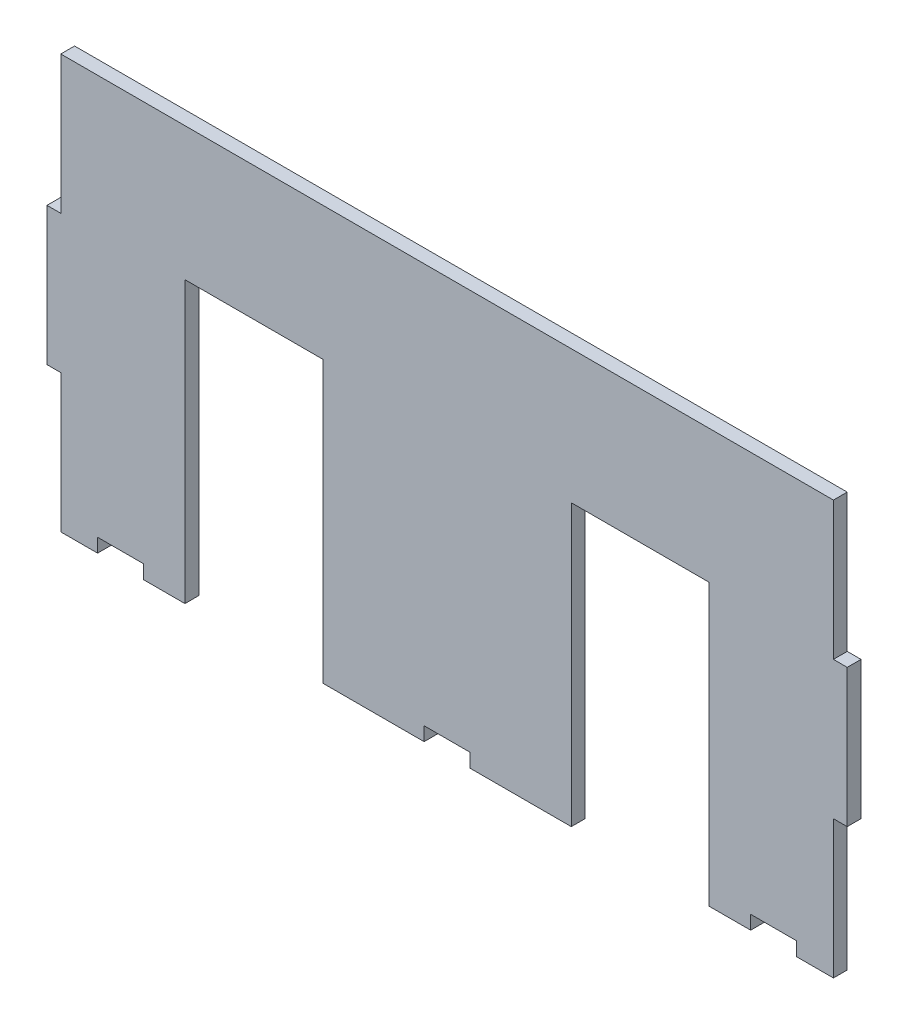
SolidWorks part; units mm, degrees
ref_plane "Front Plane" through (0, 0, 0) normal (0, 0, 1) x (1, 0, 0)
ref_plane "Top Plane" through (0, 0, 0) normal (0, 1, 0) x (1, 0, 0)
ref_plane "Right Plane" through (0, 0, 0) normal (1, 0, 0) x (0, 0, -1)
sketch "Model" plane through (0, 0, 0) normal (0, 0, 1) x (1, 0, 0)
  line L0 (178.1905, 199.1238) -> (178.1905, 169.1238)
  line L1 (352.1905, 199.1238) -> (352.1905, 169.1238)
  line L2 (322.1905, 139.1238) -> (322.1905, 200.1238)
  line L3 (322.1905, 200.1238) -> (292.1905, 200.1238)
  line L4 (292.1905, 200.1238) -> (292.1905, 139.1238)
  line L5 (181.1905, 229.1238) -> (349.1905, 229.1238)
  line L13 (181.1905, 139.1238) -> (189.1905, 139.1238)
  line L16 (189.1905, 139.1238) -> (189.1905, 142.1238)
  line L18 (189.1905, 142.1238) -> (199.1905, 142.1238)
  line L19 (208.1905, 139.1238) -> (199.1905, 139.1238)
  line L20 (199.1905, 139.1238) -> (199.1905, 142.1238)
  line L21 (238.1905, 139.1238) -> (260.1905, 139.1238)
  line L22 (260.1905, 139.1238) -> (260.1905, 142.1238)
  line L23 (260.1905, 142.1238) -> (270.1905, 142.1238)
  line L29 (292.1905, 139.1238) -> (270.1905, 139.1238)
  line L33 (238.1905, 139.1238) -> (238.1905, 200.1238)
  line L34 (270.1905, 139.1238) -> (270.1905, 142.1238)
  line L39 (322.1905, 139.1238) -> (331.1905, 139.1238)
  line L40 (331.1905, 139.1238) -> (331.1905, 142.1238)
  line L41 (238.1905, 200.1238) -> (208.1905, 200.1238)
  line L42 (208.1905, 200.1238) -> (208.1905, 139.1238)
  line L43 (208.1905, 139.1238) -> (181.1905, 139.1238) construction
  line L48 (331.1905, 142.1238) -> (341.1905, 142.1238)
  line L49 (341.1905, 142.1238) -> (341.1905, 139.1238)
  line L50 (341.1905, 139.1238) -> (349.1905, 139.1238)
  line L51 (265.1905, 142.1238) -> (265.1905, 139.1238) construction
  line L312 (292.1905, 139.1238) -> (238.1905, 139.1238) construction
  line L313 (181.1905, 139.1238) -> (181.1905, 169.1238)
  line L314 (181.1905, 169.1238) -> (178.1905, 169.1238)
  line L332 (178.1905, 199.1238) -> (181.1905, 199.1238)
  line L333 (181.1905, 199.1238) -> (181.1905, 229.1238)
  line L335 (349.1905, 229.1238) -> (349.1905, 199.1238)
  line L336 (349.1905, 199.1238) -> (352.1905, 199.1238)
  line L354 (352.1905, 169.1238) -> (349.1905, 169.1238)
  line L355 (349.1905, 169.1238) -> (349.1905, 139.1238)
  line L356 (349.1905, 139.1238) -> (322.1905, 139.1238) construction
  point P6 (265.1905, 254.1238)
  point P7 (178.1905, 232.3738)
  point P9 (352.1905, 232.3738)
  point P20 (262.9907, 139.1238)
  dimension "D2" = 27
  dimension "D3" = 30
  dimension "D4" = 30
  dimension "D5" = 3
  dimension "D6" = 3
  dimension "D7" = 30
  dimension "D8" = 30
  dimension "D9" = 30
  dimension "D10" = 30
  dimension "D11" = 168
  dimension "D12" = 30
  dimension "D13" = 61
  dimension "D14" = 3
  dimension "D15" = 3
  dimension "D16" = 3
  dimension "D17" = 8
  dimension "D18" = 10
  dimension "D19" = 10
  dimension "D20" = 8
  dimension "D21" = 84
  dimension "D25" = 30
  dimension "D26" = 27
  dimension "10" = 10
extrude "Boss-Extrude1" add sketch "Model" along normal blind 3
